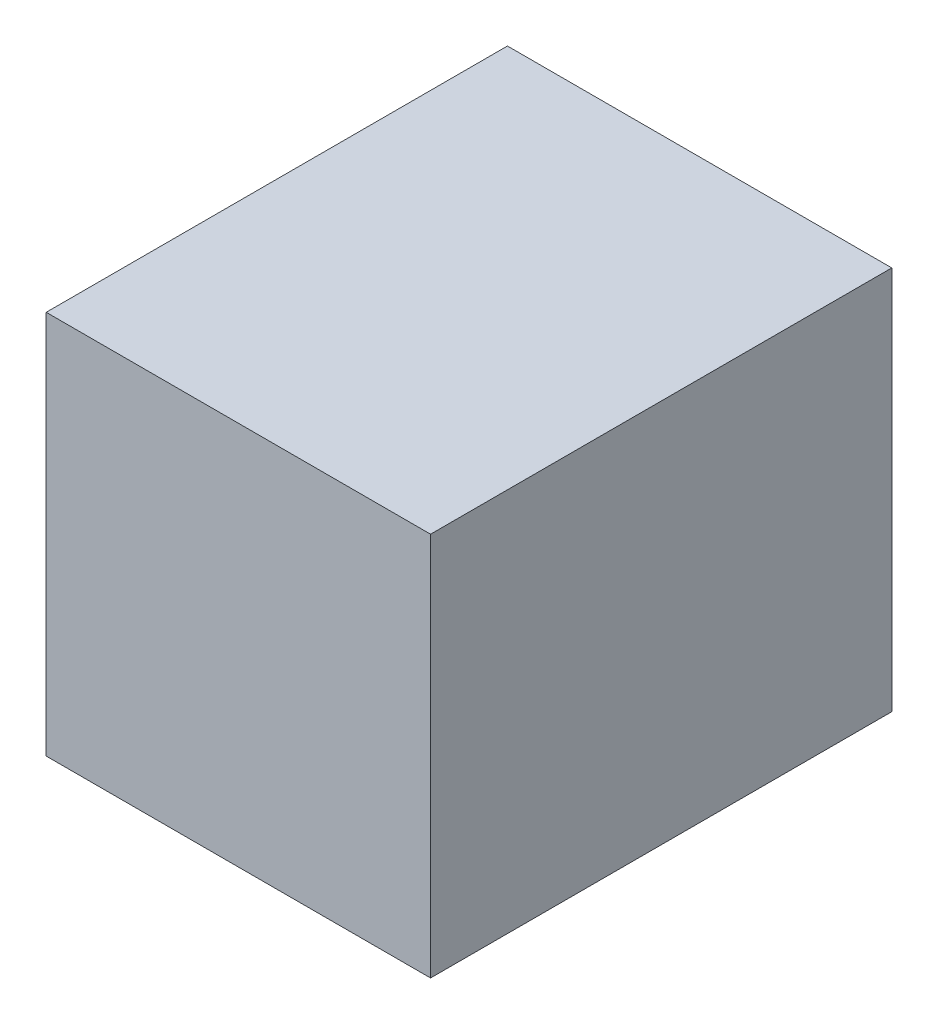
SolidWorks part; units mm, degrees
ref_plane "Front Plane" through (0, 0, 0) normal (0, 0, 1) x (1, 0, 0)
ref_plane "Top Plane" through (0, 0, 0) normal (0, 1, 0) x (1, 0, 0)
ref_plane "Right Plane" through (0, 0, 0) normal (1, 0, 0) x (0, 0, -1)
sketch "Sketch1" plane through (0, 0, 0) normal (0, 1, 0) x (1, 0, 0)
  line L1 (-125, -150) -> (125, -150)
  line L2 (-125, -150) -> (-125, 150)
  line L3 (-125, 150) -> (125, 150)
  line L4 (125, -150) -> (125, 150)
  line L5 (-125, -150) -> (125, 150) construction
  line L6 (-125, 150) -> (125, -150) construction
  point P0 (0, 0)
  dimension "D1" = 250
  dimension "D2" = 300
extrude "Boss-Extrude1" add sketch "Sketch1" along normal blind 250
